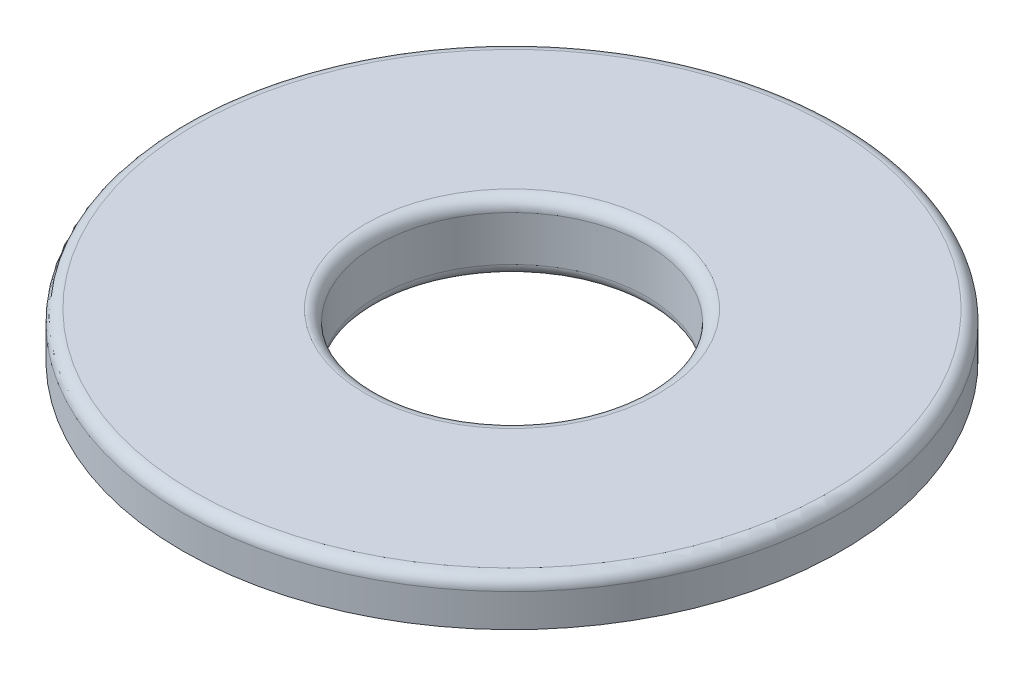
SolidWorks part; units mm, degrees
ref_plane "Front" through (0, 0, 0) normal (0, 0, 1) x (1, 0, 0)
ref_plane "Top" through (0, 0, 0) normal (0, 1, 0) x (1, 0, 0)
ref_plane "Right" through (0, 0, 0) normal (1, 0, 0) x (0, 0, -1)
sketch "Sketch1" plane through (0, 0, 0) normal (0, 1, 0) x (1, 0, 0)
  circle A0 centre (0, 0) radius 28.2575
  dimension "D1" = 56.515
extrude "Boss-Extrude1" add sketch "Sketch1" along normal blind 2.54
sketch "Sketch2" plane through (0, 2.54, 0) normal (0, 1, 0) x (1, 0, 0)
  circle A0 centre (0, 0) radius 34.925
  dimension "D1" = 69.85
extrude "Boss-Extrude2" add sketch "Sketch2" along normal blind 4.7625
sketch "Sketch3" plane through (0, 0, 0) normal (0, -1, 0) x (1, 0, 0)
  circle A0 centre (0, 0) radius 14.2875
  dimension "D1" = 28.575
extrude "Cut-Extrude1" cut sketch "Sketch3" against normal up to next
fillet "Fillet1" radius 1.27 4 edges at (0, 0, 28.2575) (0, 0, -14.2875) (0, 7.3025, 34.925) (0, 7.3025, 14.2875)
